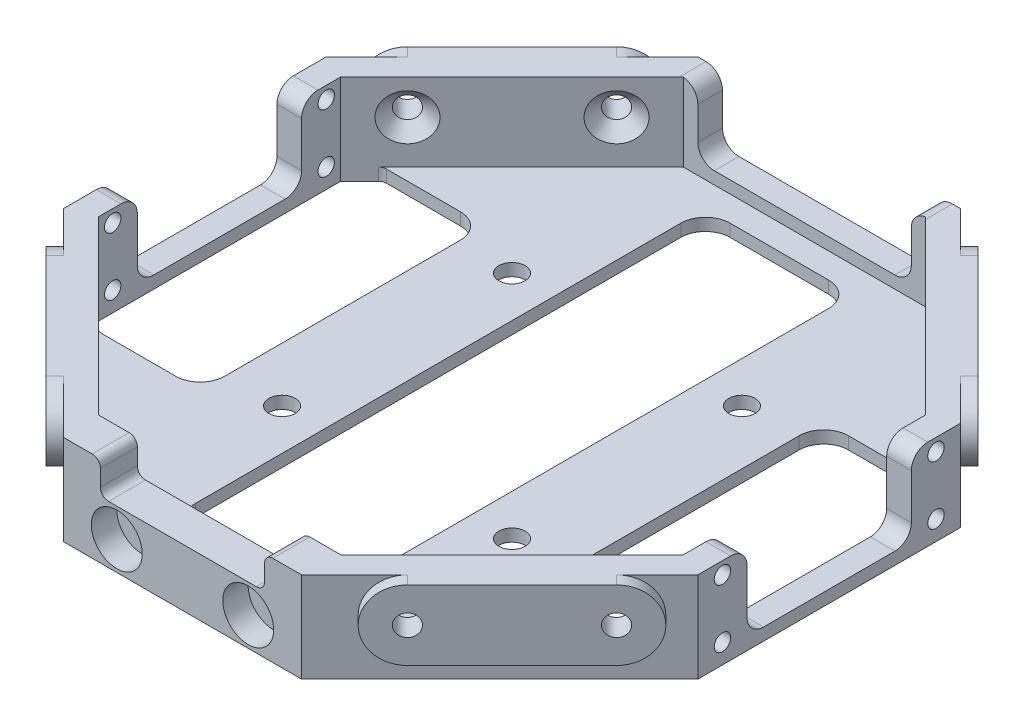
SolidWorks part; units mm, degrees
ref_plane "Front Plane" through (0, 0, 0) normal (0, 0, 1) x (1, 0, 0)
ref_plane "Top Plane" through (0, 0, 0) normal (0, 1, 0) x (1, 0, 0)
ref_plane "Right Plane" through (0, 0, 0) normal (1, 0, 0) x (0, 0, -1)
sketch "Sketch1" plane through (0, 0, 0) normal (0, 1, 0) x (1, 0, 0)
  line L1 (38.6274, 16) -> (16, 38.6274)
  line L2 (16, 38.6274) -> (-16, 38.6274)
  line L3 (-16, 38.6274) -> (-38.6274, 16)
  line L4 (-38.6274, 16) -> (-38.6274, -16)
  line L5 (-38.6274, -16) -> (-16, -38.6274)
  line L6 (-16, -38.6274) -> (16, -38.6274)
  line L7 (16, -38.6274) -> (38.6274, -16)
  line L8 (38.6274, -16) -> (38.6274, 16)
  circle A0 centre (0, 0) radius 38.6274 construction
  dimension "D1" = 32
extrude "Boss-Extrude1" add sketch "Sketch1" along normal blind 11
shell "Shell1" thickness 3
sketch "Sketch2" plane through (27.3137, 0, 27.3137) normal (0.7071, 0, 0.7071) x (0.7071, 0, -0.7071)
  line L0 (0, 11) -> (0, 6.75)
  line L1 (-16, 11) -> (16, 11) construction
  line L2 (0, 6.75) -> (9, 6.75)
  line L3 (0, 6.75) -> (-9, 6.75)
  circle A0 centre (9, 6.75) radius 1.3
  circle A1 centre (-9, 6.75) radius 1.3
extrude "Cut-Extrude1" cut sketch "Sketch2" against normal blind 152
sketch "Sketch3" plane through (-27.3137, 0, 27.3137) normal (-0.7071, 0, 0.7071) x (0.7071, 0, 0.7071)
  line L0 (0, 11) -> (0, 6.75)
  line L1 (-16, 11) -> (16, 11) construction
  line L2 (0, 6.75) -> (9, 6.75)
  line L3 (0, 6.75) -> (-9, 6.75)
  circle A0 centre (9, 6.75) radius 1.3
  circle A1 centre (-9, 6.75) radius 1.3
extrude "Cut-Extrude2" cut sketch "Sketch3" against normal blind 152
sketch "Sketch4" plane through (38.6274, 0, 0) normal (1, 0, 0) x (0, 0, -1)
  line L1 (-16, 11) -> (16, 11) construction
  line L2 (0, 1.5) -> (10, 1.5)
  line L3 (10, 1.5) -> (10, 11)
  line L4 (10, 11) -> (0, 11)
  line L5 (0, 1.5) -> (-10, 1.5)
  line L6 (-10, 1.5) -> (-10, 11)
  line L7 (-10, 11) -> (0, 11)
extrude "Cut-Extrude3" cut sketch "Sketch4" against normal blind 152
sketch "Sketch5" plane through (0, 0, -38.6274) normal (0, 0, -1) x (-1, 0, 0)
  line L0 (0, 11) -> (0, 3)
  line L1 (-16, 11) -> (16, 11) construction
  line L2 (0, 3) -> (13, 3)
  line L3 (13, 3) -> (13, 11)
  line L4 (0, 3) -> (-13, 3)
  line L5 (-13, 3) -> (-13, 11)
  line L6 (-13, 11) -> (13, 11)
  line M3 (16, 11) -> (-16, 11)
extrude "Cut-Extrude4" cut sketch "Sketch5" against normal blind 45 contours L5 L4 L0 M3 | L2 L3 L0 M3
fillet "Fillet1" radius 2 12 edges at (-13, 11, -37.1274) (-13, 3, -37.1274) (13, 11, -37.1274) (13, 3, -37.1274) (37.1274, 11, 10) (37.1274, 1.5, 10) (37.1274, 11, -10) (37.1274, 1.5, -10) (-37.1274, 11, -10) (-37.1274, 1.5, -10) (-37.1274, 11, 10) (-37.1274, 1.5, 10)
sketch "Sketch7" plane through (0, 1.5, 0) normal (0, 1, 0) x (1, 0, 0)
  line L0 (35.6274, -8) -> (35.6274, -10)
  line L1 (35.6274, -8) -> (35.6274, -10) construction
  line L2 (35.6274, -10) -> (31.6274, -10)
  line L3 (31.6274, -10) -> (31.6274, -18.7574)
  line L4 (14.7574, -35.6274) -> (35.6274, -14.7574) construction
  line L5 (31.6274, -18.7574) -> (35.6274, -14.7574)
  line L6 (35.6274, -14.7574) -> (35.6274, -10)
  line L7 (38.6274, 0) -> (-38.6274, 0)
  line L8 (38.6274, -8) -> (38.6274, 8) construction
  line L9 (-38.6274, -8) -> (-38.6274, 8) construction
  line L10 (0, 0) -> (0, 8.7153)
  line L11 (35.6274, 14.7574) -> (35.6274, 10)
  line L12 (31.6274, 18.7574) -> (35.6274, 14.7574)
  line L13 (31.6274, 10) -> (31.6274, 18.7574)
  line L14 (35.6274, 10) -> (31.6274, 10)
  line L15 (-35.6274, 10) -> (-31.6274, 10)
  line L16 (-31.6274, 10) -> (-31.6274, 18.7574)
  line L17 (-31.6274, 18.7574) -> (-35.6274, 14.7574)
  line L18 (-35.6274, 14.7574) -> (-35.6274, 10)
  line L19 (-35.6274, -14.7574) -> (-35.6274, -10)
  line L20 (-31.6274, -18.7574) -> (-35.6274, -14.7574)
  line L21 (-31.6274, -10) -> (-31.6274, -18.7574)
  line L22 (-35.6274, -10) -> (-31.6274, -10)
  line L23 (-35.6274, -8) -> (-35.6274, -10)
extrude "Cut-Extrude6" cut sketch "Sketch7" against normal blind 92
sketch "Sketch6" plane through (38.6274, 0, 0) normal (1, 0, 0) x (0, 0, -1)
  line L0 (-16, 11) -> (-13, 11)
  line L1 (-16, 11) -> (-12, 11) construction
  line L2 (-13, 11) -> (-13, 9.5)
  line L3 (-13, 9.5) -> (-13, 2.4)
  line L4 (0, 0) -> (0, 5.587)
  line L5 (13, 9.5) -> (13, 2.4)
  line L6 (13, 11) -> (13, 9.5)
  line L7 (16, 11) -> (13, 11)
  circle A0 centre (-13, 9.5) radius 1
  circle A1 centre (-13, 2.4) radius 1
  circle A2 centre (13, 2.4) radius 1
  circle A3 centre (13, 9.5) radius 1
  dimension "D1" = 1.5
  dimension "D2" = 7.1
extrude "Cut-Extrude7" cut sketch "Sketch6" against normal blind 5
sketch "Sketch12" plane through (-35.6274, 0, 0) normal (1, 0, 0) x (0, 0, -1)
  circle A0 centre (-13, 9.5) radius 1
  circle A1 centre (-13, 2.4) radius 1
  circle A2 centre (13, 2.4) radius 1
  circle A3 centre (13, 9.5) radius 1
extrude "Cut-Extrude8" cut sketch "Sketch12" against normal blind 5
fillet "Fillet2" radius 1 12 edges at (-31.6274, 0.75, 10) (-31.6274, 0.75, 18.7574) (-35.6274, 0.75, 10) (35.6274, 0.75, -10) (31.6274, 0.75, -10) (31.6274, 0.75, -18.7574) (31.6274, 0.75, 10) (35.6274, 0.75, 10) (31.6274, 0.75, 18.7574) (-31.6274, 0.75, -10) (-35.6274, 0.75, -10) (-31.6274, 0.75, -18.7574)
sketch "Sketch13" plane through (0, 11, 0) normal (0, 1, 0) x (1, 0, 0)
  line L0 (-16, -38.6274) -> (16, -38.6274)
  line L1 (16, -38.6274) -> (14.5, -40.1274)
  line L2 (0, -38.6274) -> (0, -40.1274)
  line L3 (-14.5, -40.1274) -> (14.5, -40.1274)
  line L4 (-16, -38.6274) -> (-14.5, -40.1274)
  line M12 (-16, -38.6274) -> (16, -38.6274)
extrude "Boss-Extrude2" add sketch "Sketch13" against normal blind 11 contours L4 L3 L2 M12 | L2 L3 L1 L0
sketch "Sketch14" plane through (0, 0, 40.1274) normal (0, 0, 1) x (1, 0, 0)
  line L0 (0, 0) -> (0, 3.5)
  line L1 (-14.5, 0) -> (14.5, 0) construction
  line L2 (0, 3.5) -> (8, 3.5)
  circle A0 centre (8, 3.5) radius 3.1
  circle A1 centre (-8, 3.5) radius 3.1
extrude "Cut-Extrude9" cut sketch "Sketch14" against normal blind 3.1
sketch "Sketch18" plane through (0, 0, 40.1274) normal (0, 0, 1) x (1, 0, 0)
  line L0 (-4.9, 3.5) -> (4.9, 3.5)
  line L1 (0, 3.5) -> (0, 7)
  line L2 (0, 7) -> (10, 7)
  line L3 (10, 7) -> (10, 11)
  line L4 (-14.5, 11) -> (14.5, 11) construction
  line L5 (0, 7) -> (-10, 7)
  line L6 (-10, 7) -> (-10, 11)
  line L7 (-10, 11) -> (10, 11)
  circle A0 centre (-8, 3.5) radius 3.1 construction
  circle A1 centre (-8, 3.5) radius 3.1 construction
  circle A2 centre (8, 3.5) radius 3.1 construction
  line M1 (14.5, 11) -> (-14.5, 11)
extrude "Cut-Extrude10" cut sketch "Sketch18" against normal blind 9.1 contours L6 L5 L2 L3 M1
fillet "Fillet3" radius 1 4 edges at (-10, 7, 37.8774) (-10, 11, 37.8774) (10, 11, 37.8774) (10, 7, 37.8774)
sketch "Sketch19" plane through (0, 0, 0) normal (0, -1, 0) x (-1, 0, 0)
  line L1 (9, 32.5563) -> (-9, 32.5563)
  line L2 (9, 32.5563) -> (9, -32.5563)
  line L3 (9, -32.5563) -> (-9, -32.5563)
  line L4 (-9, 32.5563) -> (-9, -32.5563)
  line L5 (9, 32.5563) -> (-9, -32.5563) construction
  line L6 (9, -32.5563) -> (-9, 32.5563) construction
  line L16 (-14, -14) -> (0, -14)
  line L34 (-20.6274, 8) -> (-20.6274, -8)
  line L38 (35.6274, 8) -> (35.6274, -8)
  line L39 (20.6274, 8) -> (20.6274, -8)
  line L41 (38.6274, -8) -> (38.6274, 8) construction
  line L43 (0, -14) -> (0, 0)
  line L45 (32.6274, 11) -> (35.6274, 11)
  line L46 (32.6274, -11) -> (35.6274, -11)
  line L47 (35.6274, -11) -> (35.6274, 11)
  line L48 (-32.6274, 11) -> (-35.6274, 11)
  line L49 (32.6274, 17.3431) -> (20.6274, 17.3431)
  line L50 (20.6274, 17.3431) -> (20.6274, 8)
  line L51 (-32.6274, -11) -> (-35.6274, -11)
  line L52 (-35.6274, -12) -> (-35.6274, -10) construction
  line L54 (32.6274, 17.3431) -> (32.6274, 11)
  line L55 (32.6274, -17.3431) -> (20.6274, -17.3431)
  line L56 (20.6274, -17.3431) -> (20.6274, -8)
  line L57 (32.6274, -11) -> (32.6274, -17.3431)
  line L58 (-32.6274, -11) -> (-32.6274, -17.3431)
  line L59 (-20.6274, -17.3431) -> (-20.6274, -8)
  line L60 (-32.6274, -17.3431) -> (-20.6274, -17.3431)
  line L61 (-32.6274, 17.3431) -> (-32.6274, 11)
  line L62 (-20.6274, 17.3431) -> (-20.6274, 8)
  line L63 (-32.6274, 17.3431) -> (-20.6274, 17.3431)
  line L65 (-32.6274, -11) -> (-35.6274, -11)
  line L66 (-32.6274, 11) -> (-35.6274, 11)
  line L67 (-20.6274, 8) -> (-20.6274, -8)
  line L69 (-35.6274, 11) -> (-35.6274, -11)
  circle A0 centre (14, -14) radius 1.6
  circle A1 centre (-14, -14) radius 1.6
  circle A2 centre (-14, 14) radius 1.6
  circle A3 centre (14, 14) radius 1.6
  arc A18 (33.3345, 17.0503) -> (31.6274, 16.3431) centre (32.6274, 16.3431) ccw construction
  arc A19 (31.6274, -16.3431) -> (33.3345, -17.0503) centre (32.6274, -16.3431) ccw construction
  point P12 (0, 0)
  dimension "D2" = 3
extrude "Cut-Extrude12" cut sketch "Sketch19" against normal blind 10
fillet "Fillet4" radius 3 8 edges at (-9, 0.75, -32.5563) (9, 0.75, -32.5563) (9, 0.75, 32.5563) (-9, 0.75, 32.5563) (-20.6274, 0.75, -17.3431) (20.6274, 0.75, -17.3431) (20.6274, 0.75, 17.3431) (-20.6274, 0.75, 17.3431)
chamfer "Chamfer1" distance 1.5 angle 45 8 edges at (17.9092, 6.75, 32.4756) (-30.6371, 6.75, -19.7477) (30.6371, 6.75, 19.7477) (-17.9092, 6.75, -32.4756) (-19.7477, 6.75, 30.6371) (32.4756, 6.75, -17.9092) (-32.4756, 6.75, 17.9092) (19.7477, 6.75, -30.6371)
sketch "Sketch20" plane through (27.3137, 0, 27.3137) normal (0.7071, 0, 0.7071) x (0.7071, 0, -0.7071)
  line L0 (-9, 2.5) -> (9, 2.5)
  line L1 (9, 11) -> (-9, 11)
  arc A0 (-9, 11) -> (-9, 2.5) centre (-9, 6.75) ccw
  arc A1 (9, 2.5) -> (9, 11) centre (9, 6.75) ccw
  circle A2 centre (-9, 6.75) radius 1.3
  circle A3 centre (9, 6.75) radius 1.3
extrude "Boss-Extrude3" add sketch "Sketch20" along normal blind 1.5
mirror "Mirror1" about plane through (0, 0, 0) normal (1, 0, 0) of "Boss-Extrude3" second plane through (0, 0, 0) second plane normal (0, 0, 1)
